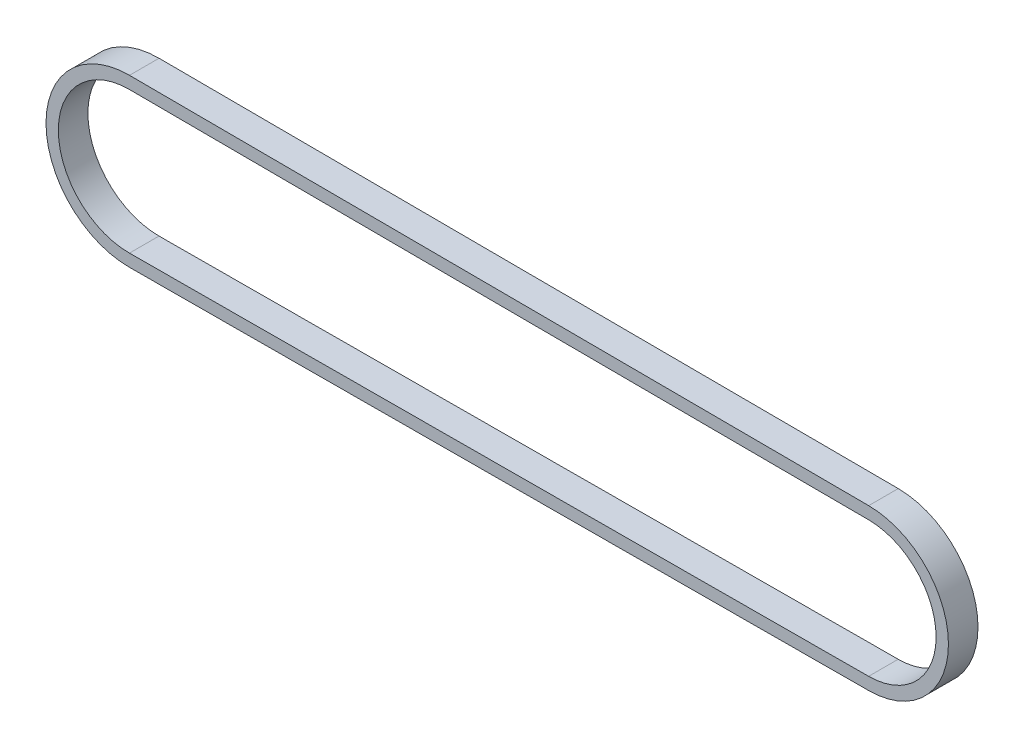
SolidWorks part; units mm, degrees
ref_plane "Front Plane" through (0, 0, 0) normal (0, 0, 1) x (1, 0, 0)
ref_plane "Top Plane" through (0, 0, 0) normal (0, 1, 0) x (1, 0, 0)
ref_plane "Right Plane" through (0, 0, 0) normal (1, 0, 0) x (0, 0, -1)
sketch "Sketch2" plane through (0, 0, 0) normal (0, 0, 1) x (1, 0, 0)
  line L0 (0, 0) -> (1, 0) construction
  line L1 (0, 0) -> (0, 1) construction
  line L2 (0.026, 6.2499) -> (60.025, 5.9999)
  line L3 (60.025, -5.9999) -> (0.026, -6.2499)
  arc A0 (0.026, -6.2499) -> (0.026, 6.2499) centre (0, 0) cw
  arc A1 (60.025, 5.9999) -> (60.025, -5.9999) centre (60, 0) cw
sketch "Sketch4" plane through (0, 0, 0) normal (1, 0, 0) x (0, 0, -1)
  line L0 (0, 6.25) -> (0, -6.25) construction
  line L1 (1.2, 5.75) -> (-1.2, 5.75)
  line L2 (1.2, 5.75) -> (1.2, 6.75)
  line L3 (1.2, 6.75) -> (-1.2, 6.75)
  line L4 (-1.2, 5.75) -> (-1.2, 6.75)
  line L5 (1.2, 5.75) -> (-1.2, 6.75) construction
  line L6 (1.2, 6.75) -> (-1.2, 5.75) construction
  point P0 (0, 6.25)
  dimension "D1" = 1
  dimension "D2" = 2.4
sweep "Sweep2" add profiles "Sketch4" path "Sketch2"
